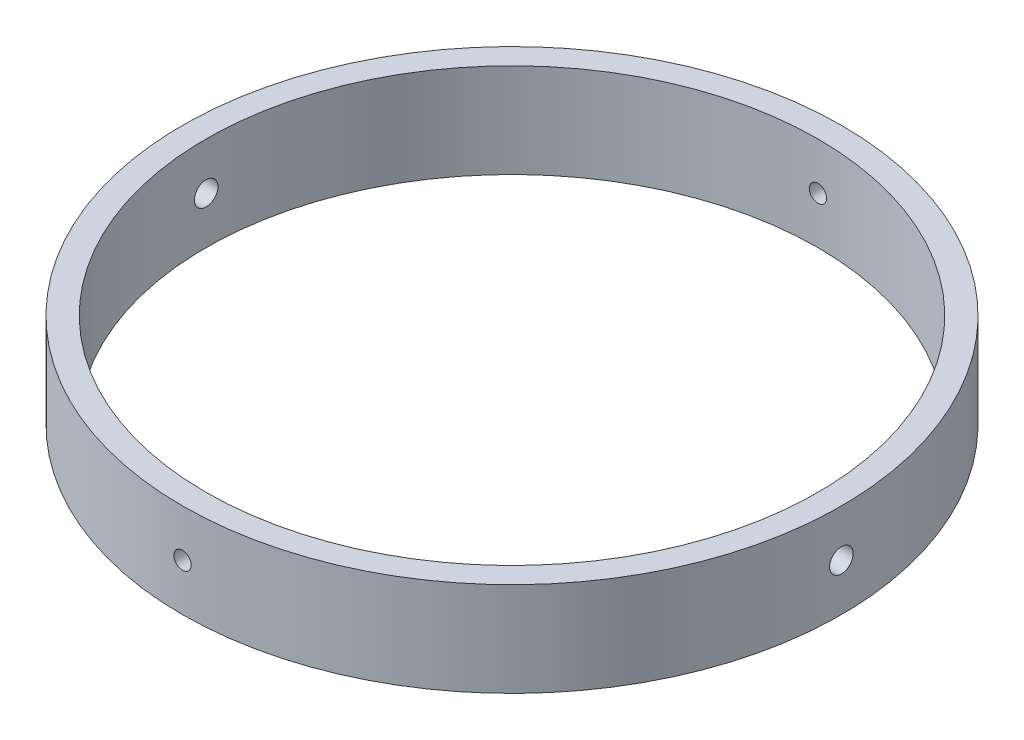
SolidWorks part; units mm, degrees
ref_plane "Front Plane" through (0, 0, 0) normal (0, 0, 1) x (1, 0, 0)
ref_plane "Top Plane" through (0, 0, 0) normal (0, 1, 0) x (1, 0, 0)
ref_plane "Right Plane" through (0, 0, 0) normal (1, 0, 0) x (0, 0, -1)
sketch "Sketch1" plane through (0, 0, 0) normal (0, 1, 0) x (1, 0, 0)
  circle A0 centre (0, 0) radius 88.9
  circle A1 centre (0, 0) radius 82.55
  dimension "D1" = 177.8
  dimension "D2" = 165.1
extrude "Boss-Extrude1" add sketch "Sketch1" along normal blind 25.4
sketch "Sketch2" plane through (0, 0, 0) normal (1, 0, 0) x (0, 0, -1)
  circle A0 centre (0, 12.7) radius 3.175
  dimension "D1" = 6.35
extrude "Cut-Extrude1" cut sketch "Sketch2" against normal through all and the other way through all
sketch "Sketch3" plane through (0, 0, 0) normal (0, 0, 1) x (1, 0, 0)
  circle A0 centre (0, 12.7) radius 2.3368
  dimension "D1" = 4.6736
extrude "Cut-Extrude2" cut sketch "Sketch3" against normal through all and the other way through all
